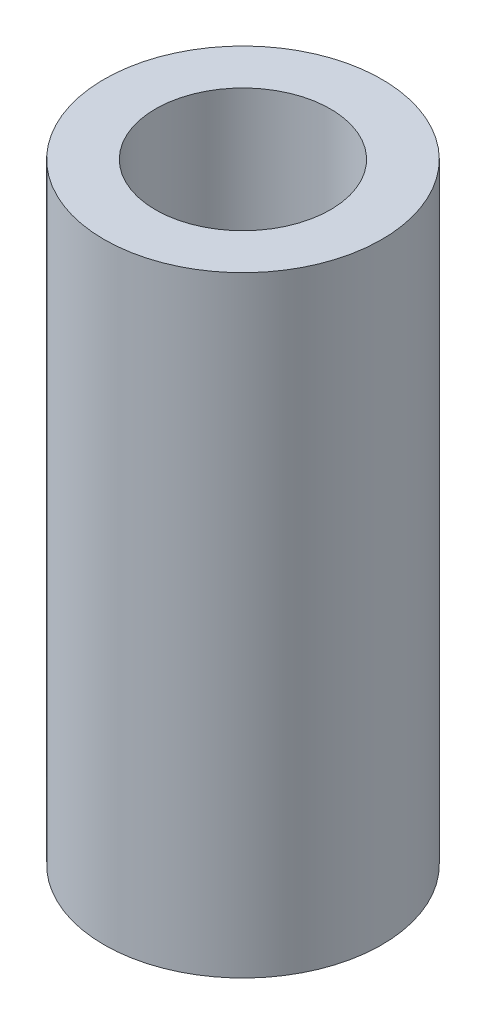
SolidWorks part; units mm, degrees
material "6061-T6 (SS)"
ref_plane "X-Y Datum" through (0, 0, 0) normal (0, 0, 1) x (1, 0, 0)
ref_plane "X-Z Datum" through (0, 0, 0) normal (0, 1, 0) x (1, 0, 0)
ref_plane "Y-Z Datum" through (0, 0, 0) normal (1, 0, 0) x (0, 0, -1)
sketch "Sketch1" plane through (0, 0, 0) normal (0, 1, 0) x (1, 0, 0)
  circle A0 centre (0, 0) radius 2
  circle A1 centre (0, 0) radius 3.175
  dimension "D1" = 4
  dimension "D2" = 6.35
extrude "Boss-Extrude1" add sketch "Sketch1" against normal blind 13.97
